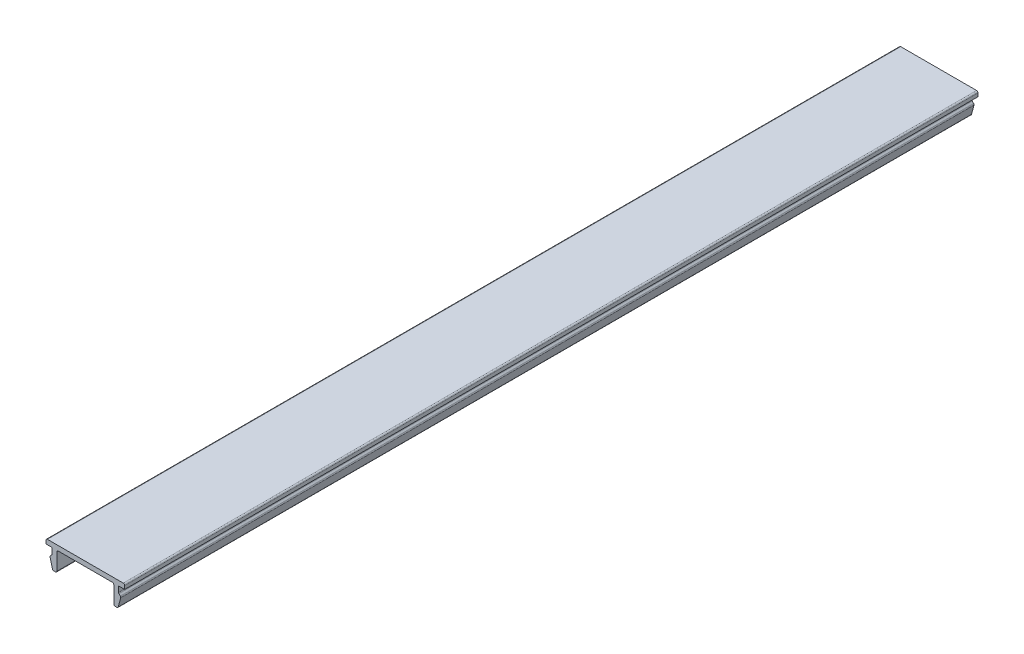
SolidWorks part; units mm, degrees
material "ABS"
ref_plane "Plano frontal" through (0, 0, 0) normal (0, 0, 1) x (1, 0, 0)
ref_plane "Plano superior" through (0, 0, 0) normal (0, 1, 0) x (1, 0, 0)
ref_plane "Plano direito" through (0, 0, 0) normal (1, 0, 0) x (0, 0, -1)
sketch "Sketch1" plane through (0, 0, 0) normal (0, 0, 1) x (1, 0, 0)
  line L0 (-8.3, 1) -> (8.3, 1)
  line L1 (-8.3, 0) -> (-7, 0)
  line L2 (-8.3, 1) -> (-8.3, 0)
  line L3 (8.3, 1) -> (8.3, 0)
  line L4 (-7, 0) -> (-7, -1.3)
  line L5 (-7, -1.3) -> (-7.5, -1.8)
  line L6 (-7.5, -1.8) -> (-6.8837, -4.1)
  line L7 (-6, 0) -> (-6, -4.1)
  line L8 (-6, -4.1) -> (-6.8837, -4.1)
  line L9 (0, 0) -> (0, -1.7195) construction
  line L10 (6, -4.1) -> (6.8837, -4.1)
  line L11 (6, 0) -> (6, -4.1)
  line L12 (7.5, -1.8) -> (6.8837, -4.1)
  line L13 (7, -1.3) -> (7.5, -1.8)
  line L14 (7, 0) -> (7, -1.3)
  line L15 (7, 0) -> (8.3, 0)
  line L16 (-8.3, 0) -> (8.3, 0) construction
  line L17 (-6, 0) -> (6, 0)
  point P21 (0, 1)
  dimension "D1" = 16.6
  dimension "D3" = 1.3
  dimension "D4" = 1.3
  dimension "D5" = 135
  dimension "D6" = 120
  dimension "D7" = 4.1
  dimension "D8" = 0.5
  dimension "D9" = 1
  dimension "D2" = 1
extrude "Boss-Extrude1" add sketch "Sketch1" along normal blind 180
fillet "Fillet1" radius 0.3 12 edges at (8.3, 1, 90) (7, -1.3, 90) (7.5, -1.8, 90) (6.8837, -4.1, 90) (6, -4.1, 90) (6, 0, 90) (-6, 0, 90) (-6, -4.1, 90) (-6.8837, -4.1, 90) (-7.5, -1.8, 90) (-7, -1.3, 90) (-8.3, 1, 90)
